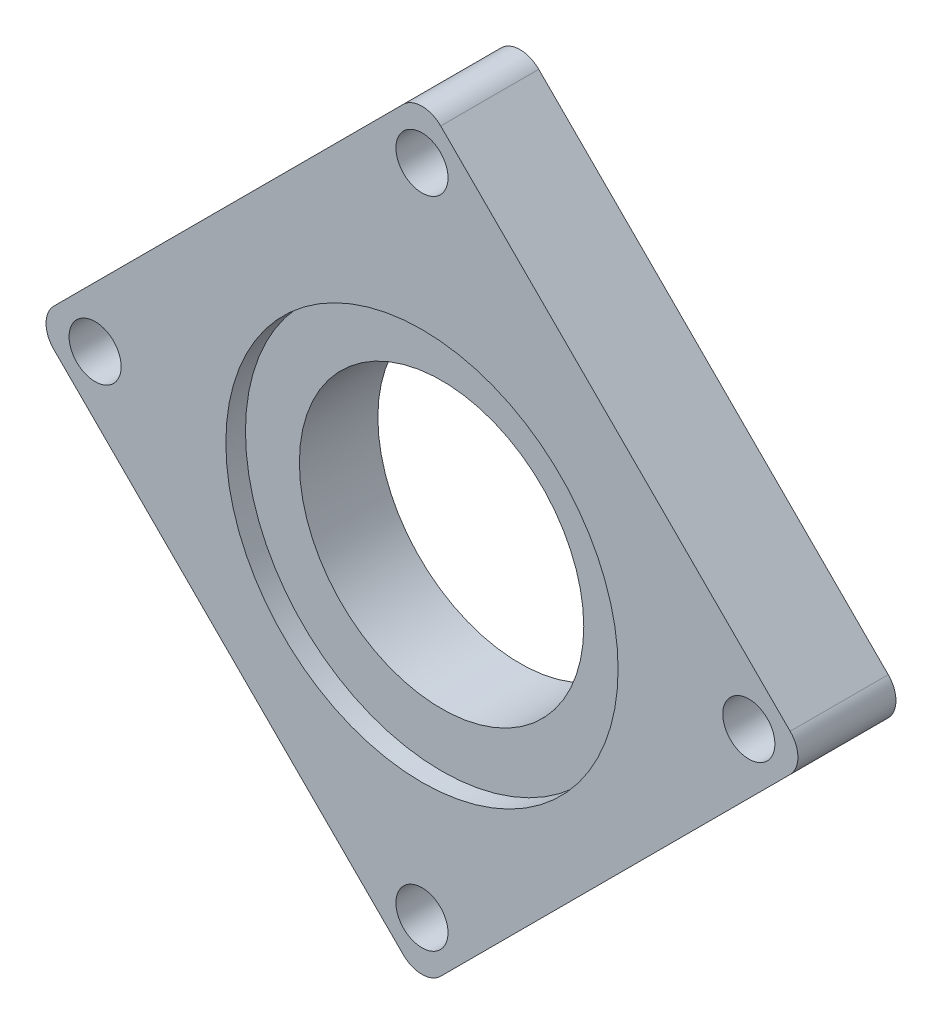
SolidWorks part; units mm, degrees
ref_plane "Front Plane" through (0, 0, 0) normal (0, 0, 1) x (1, 0, 0)
ref_plane "Top Plane" through (0, 0, 0) normal (0, 1, 0) x (1, 0, 0)
ref_plane "Right Plane" through (0, 0, 0) normal (1, 0, 0) x (0, 0, -1)
sketch "Sketch1" plane through (0, 0, 0) normal (0, 0, 1) x (1, 0, 0)
  line L48 (96.4567, 48.3669) -> (64.849, 79.9745)
  line L49 (92.4262, 40.518) -> (96.4567, 44.5485)
  line L52 (60.8185, 8.9103) -> (92.4262, 40.518)
  line L53 (52.9697, 12.9408) -> (57.0002, 8.9103)
  line L56 (21.362, 44.5485) -> (52.9697, 12.9408)
  line L57 (25.3925, 52.3974) -> (21.362, 48.3669)
  line L60 (57.0002, 84.0051) -> (25.3925, 52.3974)
  line L61 (64.849, 79.9745) -> (60.8185, 84.0051)
  circle A0 centre (58.9094, 45.0773) radius 14.5
  circle A12 centre (58.9094, 13.1247) radius 2.6556
  circle A13 centre (92.2424, 46.4577) radius 2.6556
  circle A14 centre (58.9094, 79.7907) radius 2.6556
  circle A15 centre (25.5763, 46.4577) radius 2.6556
  arc A31 (96.4567, 44.5485) -> (96.4567, 48.3669) centre (94.5475, 46.4577) ccw
  arc A33 (57.0002, 8.9103) -> (60.8185, 8.9103) centre (58.9094, 10.8195) ccw
  arc A35 (21.362, 48.3669) -> (21.362, 44.5485) centre (23.2712, 46.4577) ccw
  arc A37 (60.8185, 84.0051) -> (57.0002, 84.0051) centre (58.9094, 82.0959) ccw
  dimension "D1" = 29
extrude "Boss-Extrude1" add sketch "Sketch1" along normal blind 10
sketch "Sketch2" plane through (0, 0, 10) normal (0, 0, 1) x (1, 0, 0)
  circle A0 centre (58.9094, 45.0773) radius 20
extrude "Cut-Extrude1" cut sketch "Sketch2" against normal blind 2
